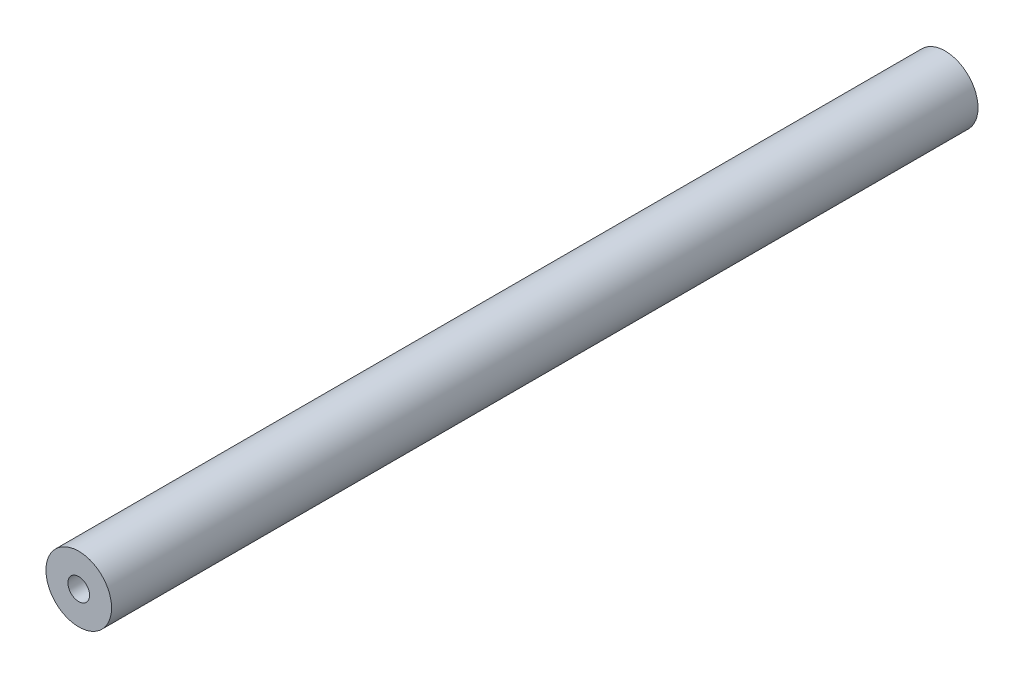
SolidWorks part; units mm, degrees
ref_plane "Alzado" through (0, 0, 0) normal (0, 0, 1) x (1, 0, 0)
ref_plane "Planta" through (0, 0, 0) normal (0, 1, 0) x (1, 0, 0)
ref_plane "Vista lateral" through (0, 0, 0) normal (1, 0, 0) x (0, 0, -1)
sketch "Croquis2" plane through (0, 0, 0) normal (0, 0, 1) x (1, 0, 0)
  circle A0 centre (0, 0) radius 12.5
  circle A1 centre (0, 0) radius 37.875
  dimension "D1" = 25
  dimension "D2" = 75.75
extrude "Saliente-Extruir1" add sketch "Croquis2" along normal blind 1000
